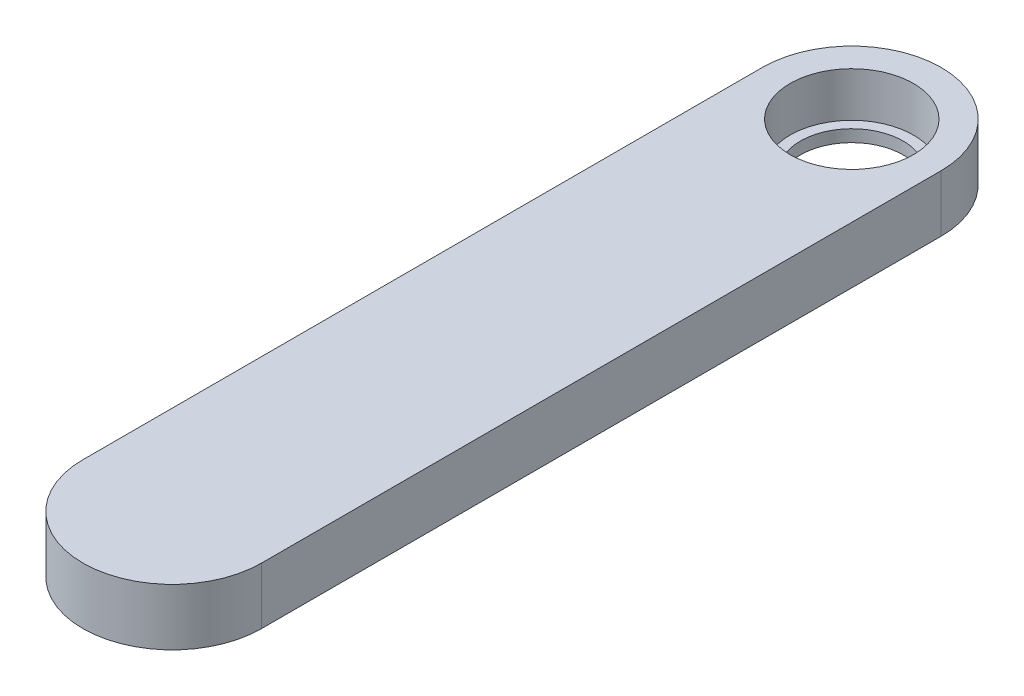
SolidWorks part; units mm, degrees
material "6061-T6 (SS)"
ref_plane "Front Plane" through (0, 0, 0) normal (0, 0, 1) x (1, 0, 0)
ref_plane "Top Plane" through (0, 0, 0) normal (0, 1, 0) x (1, 0, 0)
ref_plane "Right Plane" through (0, 0, 0) normal (1, 0, 0) x (0, 0, -1)
sketch "Sketch1" plane through (0, 0, 0) normal (0, 1, 0) x (1, 0, 0)
  line L1 (5, -19) -> (-5, -19)
  line L2 (5, -19) -> (5, 19)
  line L3 (5, 19) -> (-5, 19)
  line L4 (-5, -19) -> (-5, 19)
  line L5 (5, -19) -> (-5, 19) construction
  line L6 (5, 19) -> (-5, -19) construction
  arc A0 (-5, 19) -> (5, 19) centre (0, 19) cw
  arc A1 (-5, -19) -> (5, -19) centre (0, -19) ccw
  point P0 (0, 0)
  dimension "D1" = 10
  dimension "D2" = 38
extrude "Boss-Extrude1" add sketch "Sketch1" along normal mid plane 3.175 contours A0 L3 | L4 L1 L2 L3 | L1 A1
sketch "Sketch2" plane through (0, 1.5875, 0) normal (0, 1, 0) x (1, 0, 0)
  circle A0 centre (0, 19) radius 3.45
  dimension "D1" = 6.9
extrude "Cut-Extrude1" cut sketch "Sketch2" against normal blind 2.5
sketch "Sketch3" plane through (0, -0.9125, 0) normal (0, 1, 0) x (1, 0, 0)
  circle A0 centre (0, 19) radius 2.875
  dimension "D1" = 5.75
extrude "Cut-Extrude2" cut sketch "Sketch3" against normal through all
